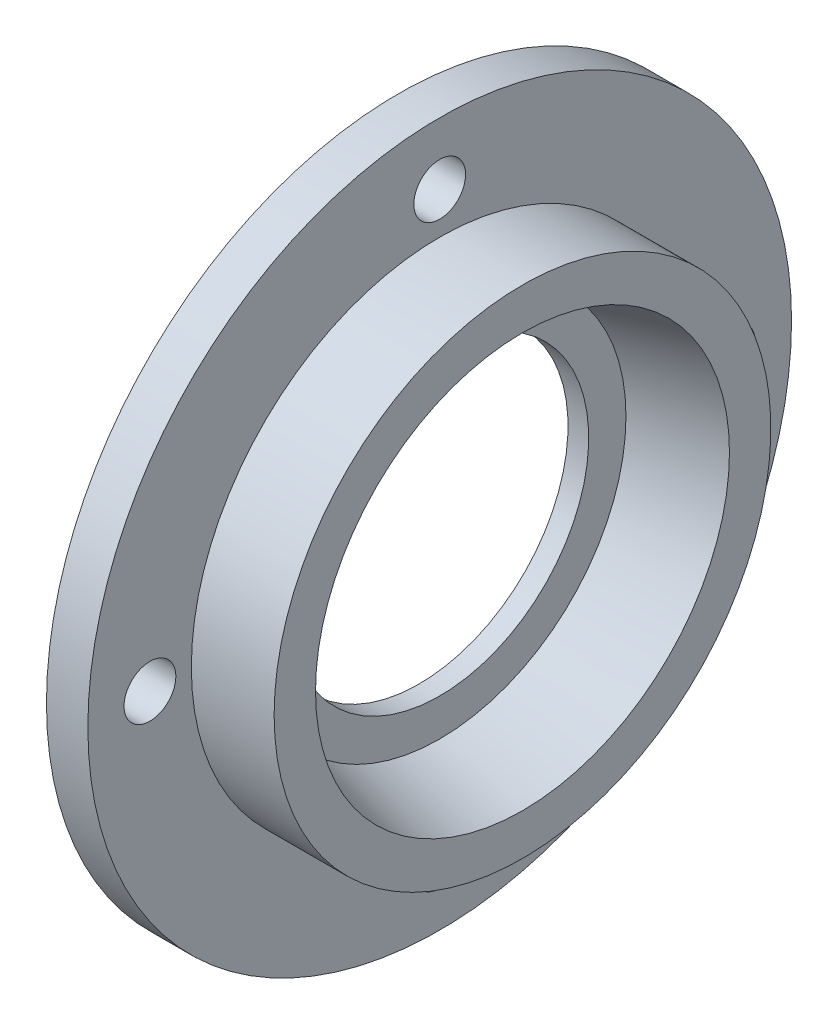
SolidWorks part; units mm, degrees
material "Alloy Steel (SS)"
ref_plane "Front Plane" through (0, 0, 0) normal (0, 0, 1) x (1, 0, 0)
ref_plane "Top Plane" through (0, 0, 0) normal (0, 1, 0) x (1, 0, 0)
ref_plane "Right Plane" through (0, 0, 0) normal (1, 0, 0) x (0, 0, -1)
sketch "Sketch1" plane through (0, 0, 0) normal (0, 0, 1) x (1, 0, 0)
  line L0 (0, 0) -> (24.9927, 0) construction
  line L1 (0, 0) -> (0, 17)
  line L2 (0, 17) -> (2, 17)
  line L3 (2, 17) -> (2, 12)
  line L4 (2, 12) -> (6, 12)
  line L5 (6, 12) -> (6, 10)
  line L7 (2, 9) -> (2, 0)
  line L8 (2, 0) -> (0, 0)
  line L9 (6, 10) -> (2, 9)
  point P5 (6, 11)
  dimension "D1" = 12
  dimension "D2" = 10
  dimension "D3" = 17
  dimension "2" = 2
  dimension "D5" = 4
  dimension "D6" = 9
revolve "Revolve1" add sketch "Sketch1" angle 360 about L0
sketch "Sketch2" plane through (0, 0, 0) normal (-1, 0, 0) x (0, 0, 1)
  circle A0 centre (0, 0) radius 12
  circle A2 centre (0, 0) radius 17 construction
  dimension "D1" = 5
sketch "Sketch4" plane through (0, 0, 0) normal (-1, 0, 0) x (0, 0, 1)
  circle A0 centre (0, 0) radius 14 construction
  circle A1 centre (0, 14) radius 1.25
  circle A2 centre (14, 0) radius 1.25
  circle A3 centre (0, -14) radius 1.25
  circle A4 centre (-14, 0) radius 1.25
  circle A5 centre (0, 0) radius 17 construction
  dimension "D1" = 3
  dimension "D2" = 2.5
extrude "Cut-Extrude3" cut sketch "Sketch4" against normal up to next
extrude "Cut-Extrude4" cut sketch "Sketch2" against normal blind 1
sketch "Sketch5" plane through (1, 0, 0) normal (-1, 0, 0) x (0, 0, 1)
  circle A0 centre (0, 0) radius 7.2
  dimension "D1" = 14.4
extrude "Cut-Extrude5" cut sketch "Sketch5" against normal up to next
